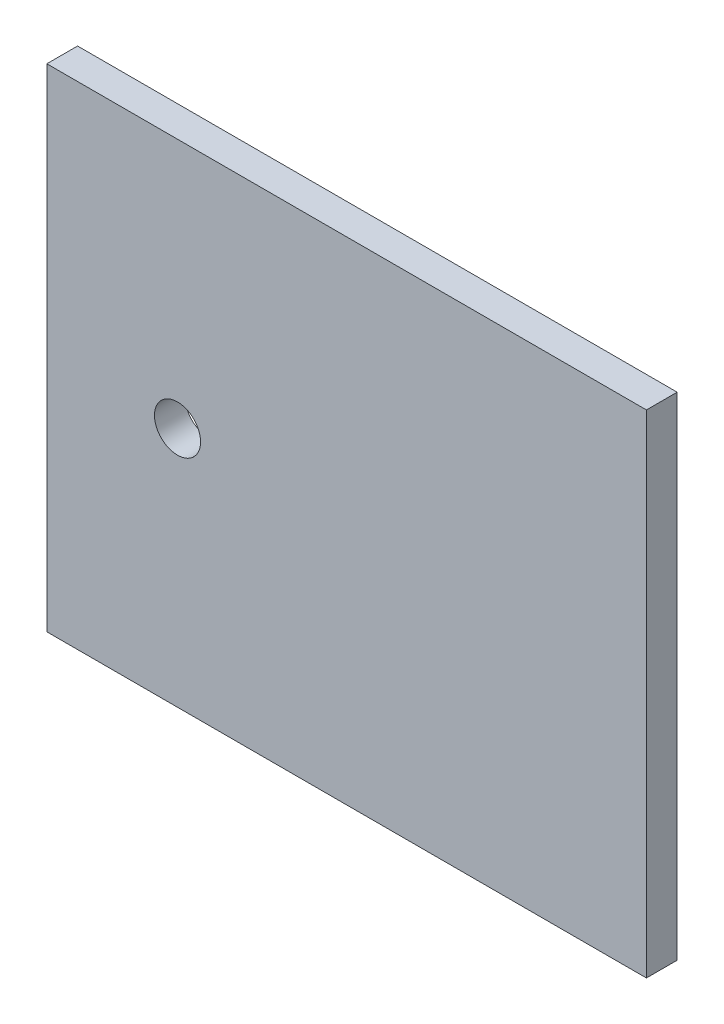
SolidWorks part; units mm, degrees
ref_plane "Front Plane" through (0, 0, 0) normal (0, 0, 1) x (1, 0, 0)
ref_plane "Top Plane" through (0, 0, 0) normal (0, 1, 0) x (1, 0, 0)
ref_plane "Right Plane" through (0, 0, 0) normal (1, 0, 0) x (0, 0, -1)
sketch "Sketch1" plane through (0, 0, 0) normal (0, 0, 1) x (1, 0, 0)
  line L1 (0, 0) -> (39, 0)
  line L2 (0, 0) -> (0, 32)
  line L3 (0, 32) -> (39, 32)
  line L4 (39, 0) -> (39, 32)
  circle A0 centre (8.5, 15.7) radius 1.5
  dimension "D5" = 3
  dimension "D1" = 32
  dimension "D2" = 39
  dimension "D3" = 8.5
  dimension "D4" = 15.7
extrude "Boss-Extrude1" add sketch "Sketch1" along normal blind 2
